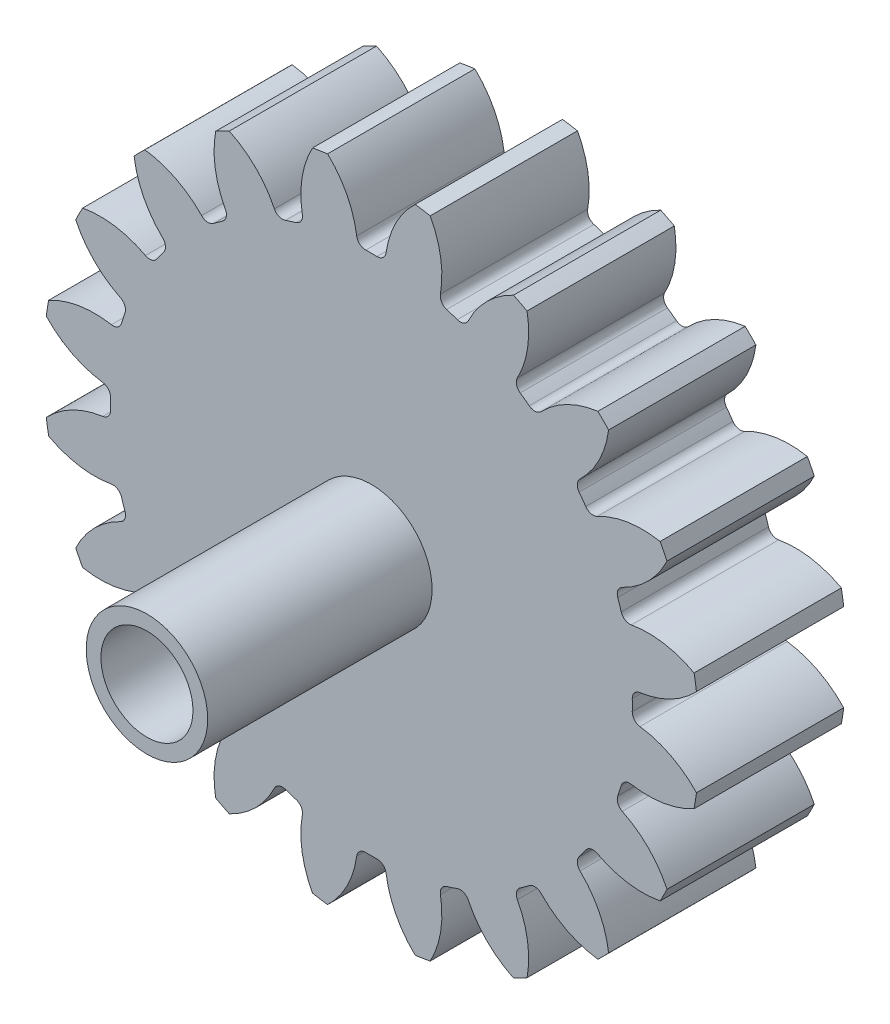
SolidWorks part; units mm, degrees
material "Custom Plastic"
ref_plane "Front Plane" through (0, 0, 0) normal (0, 0, 1) x (1, 0, 0)
ref_plane "Top Plane" through (0, 0, 0) normal (0, 1, 0) x (1, 0, 0)
ref_plane "Right Plane" through (0, 0, 0) normal (1, 0, 0) x (0, 0, -1)
sketch "Sketch1" plane through (0, 0, 0) normal (0, 0, 1) x (1, 0, 0)
  circle A0 centre (0, 0) radius 20.25
  circle A1 centre (0, 0) radius 22.275
  circle A2 centre (0, 0) radius 17.7188
  dimension "D1" = 40.5
  dimension "D3" = 35.4375
  dimension "D2" = 2.025
extrude "Boss-Extrude1" add sketch "Sketch1" along normal blind 10 contours A1
sketch "Sketch2" plane through (0, 0, 0) normal (0, 0, 1) x (1, 0, 0)
  line L0 (0, 0) -> (0, 22.275) construction
  line L1 (-1.5888, 20.1876) -> (1.5888, 20.1876) construction
  line L2 (-0.9452, 17.6935) -> (0, 0) construction
  line L3 (-2.3228, 22.3044) -> (0, 15.9226) construction
  line L4 (0, 0) -> (3.4846, 22.0008) construction
  line L5 (1.5888, 20.1876) -> (4.7273, 19.6905) construction
  circle A0 centre (0, 0) radius 22.275 construction
  arc A1 (-3.1164, 22.2074) -> (-0.9452, 17.6935) centre (-7.4448, 17.3463) cw
  arc A2 (3.1164, 22.2074) -> (0.9452, 17.6935) centre (7.4448, 17.3463) ccw
  circle A3 centre (0, 0) radius 17.7188 construction
  arc A4 (0.9452, 17.6935) -> (-0.9452, 17.6935) centre (0, 0) ccw
  circle A7 centre (0, 0) radius 20.25 construction
  circle A8 centre (0, 0) radius 22.425
  arc A9 (3.1164, 22.2074) -> (-3.1164, 22.2074) centre (0, 0) ccw
  circle A10 centre (0, 0) radius 22.275 construction
  dimension "D2" = 20
  dimension "D3" = 9
  dimension "D1" = 0.15
extrude "Cut-Extrude1" cut sketch "Sketch2" along normal through all
fillet "Fillet1" radius 0.6075 2 edges at (0.9452, 17.6935, 5) (-0.9452, 17.6935, 5)
pattern_circular "CirPattern5" count 20 over 360 about axis through (0, 0, 0) along (0, 0, 1) of "Cut-Extrude1", "Fillet1"
sketch "Sketch3" plane through (0, 0, 10) normal (0, 0, 1) x (1, 0, 0)
  circle A0 centre (0, 0) radius 2.625
  dimension "D1" = 5.25
extrude "Cut-Extrude2" cut sketch "Sketch3" against normal blind 10
sketch "Sketch4" plane through (0, 0, 10) normal (0, 0, 1) x (1, 0, 0)
  circle A0 centre (0, 0) radius 2.625 construction
  circle A1 centre (0, 0) radius 2.625
  circle A2 centre (0, 0) radius 4.125
  dimension "D1" = 1.5
extrude "Boss-Extrude2" add sketch "Sketch4" along normal blind 1
sketch "Sketch5" plane through (0, 0, 0) normal (0, 0, -1) x (-1, 0, 0)
  line L1 (0.518, -2.5734) -> (-2.5219, -0.7284)
  circle A2 centre (0, 0) radius 2.625 construction
  arc A3 (-2.5219, -0.7284) -> (0.518, -2.5734) centre (0, 0) ccw
  dimension "D1" = 3.556
sketch "Sketch6" plane through (0, 0, 10) normal (0, 0, 1) x (1, 0, 0)
  circle A0 centre (0, 0) radius 4.125 construction
  circle A1 centre (0, 0) radius 4.125
  circle A2 centre (0, 0) radius 3.125
  dimension "D1" = 1
extrude "Boss-Extrude4" add sketch "Sketch6" along normal blind 15.24
extrude "Boss-Extrude5" add sketch "Sketch5" against normal up to surface (11 mm away) up to face at (2.625, 0, 11)
equation "\"Reference Diameter\"= 40.5mm"
equation "\"Pressure Angle\"= 20'Degrees"
equation "\"number of teeth\"= 20"
equation "\"module\"= \"Reference Diameter\" / \"number of teeth\""
equation "\"base diameter\"= \"Reference Diameter\" * cos ( \"Pressure Angle\" )"
equation "\"addendum\"= \"module\""
equation "\"tooth depth\"= 2.25 * \"module\""
equation "\"tip diameter\"= \"Reference Diameter\" + 2 * \"module\""
equation "\"root diameter\"= \"Reference Diameter\" - 2.5 * \"module\""
equation "\"D1@Sketch1\"=\"Reference Diameter\""
equation "\"D2@Sketch1\"=\"addendum\""
equation "\"D3@Sketch1\"=\"root diameter\""
equation "\"D3@Sketch2\"=180 / \"number of teeth\""
equation "\"D1@Fillet1\"=0.3 * \"module\""
